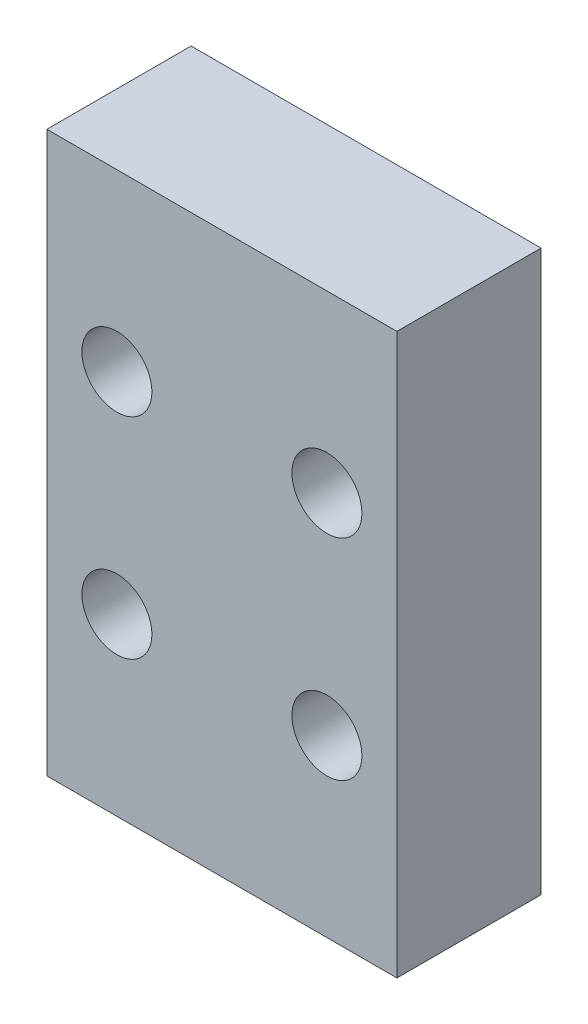
SolidWorks part; units mm, degrees
ref_plane "Front Plane" through (0, 0, 0) normal (0, 0, 1) x (1, 0, 0)
ref_plane "Top Plane" through (0, 0, 0) normal (0, 1, 0) x (1, 0, 0)
ref_plane "Right Plane" through (0, 0, 0) normal (1, 0, 0) x (0, 0, -1)
sketch "Sketch1" plane through (0, 0, 0) normal (0, 0, 1) x (1, 0, 0)
  line L1 (0, 0) -> (31.75, 0)
  line L2 (0, 0) -> (0, 50.8)
  line L3 (0, 50.8) -> (31.75, 50.8)
  line L4 (31.75, 0) -> (31.75, 50.8)
  dimension "D1" = 31.75
  dimension "D2" = 50.8
extrude "Boss-Extrude1" add sketch "Sketch1" along normal blind 13.081
sketch "Sketch2" plane through (0, 0, 13.081) normal (0, 0, 1) x (1, 0, 0)
  line L0 (31.75, 0) -> (31.75, 50.8) construction
  line L2 (0, 0) -> (31.75, 0) construction
  line L18 (6.35, 15.875) -> (25.4, 15.875) construction
  line L19 (6.35, 15.875) -> (6.35, 34.925) construction
  line L20 (6.35, 34.925) -> (25.4, 34.925) construction
  line L21 (25.4, 15.875) -> (25.4, 34.925) construction
  line L22 (6.35, 15.875) -> (25.4, 34.925) construction
  line L23 (6.35, 34.925) -> (25.4, 15.875) construction
  line L24 (31.75, 25.4) -> (0, 25.4) construction
  line L25 (0, 50.8) -> (0, 0) construction
  circle A0 centre (25.4, 34.925) radius 3.175
  circle A1 centre (6.35, 34.925) radius 3.175
  circle A2 centre (6.35, 15.875) radius 3.175
  circle A3 centre (25.4, 15.875) radius 3.175
  point P9 (15.875, 25.4)
  dimension "D4" = 25.4
  dimension "D2" = 19.05
  dimension "D3" = 6.35
  dimension "D1" = 6.35
extrude "Cut-Extrude1" cut sketch "Sketch2" against normal up to next
